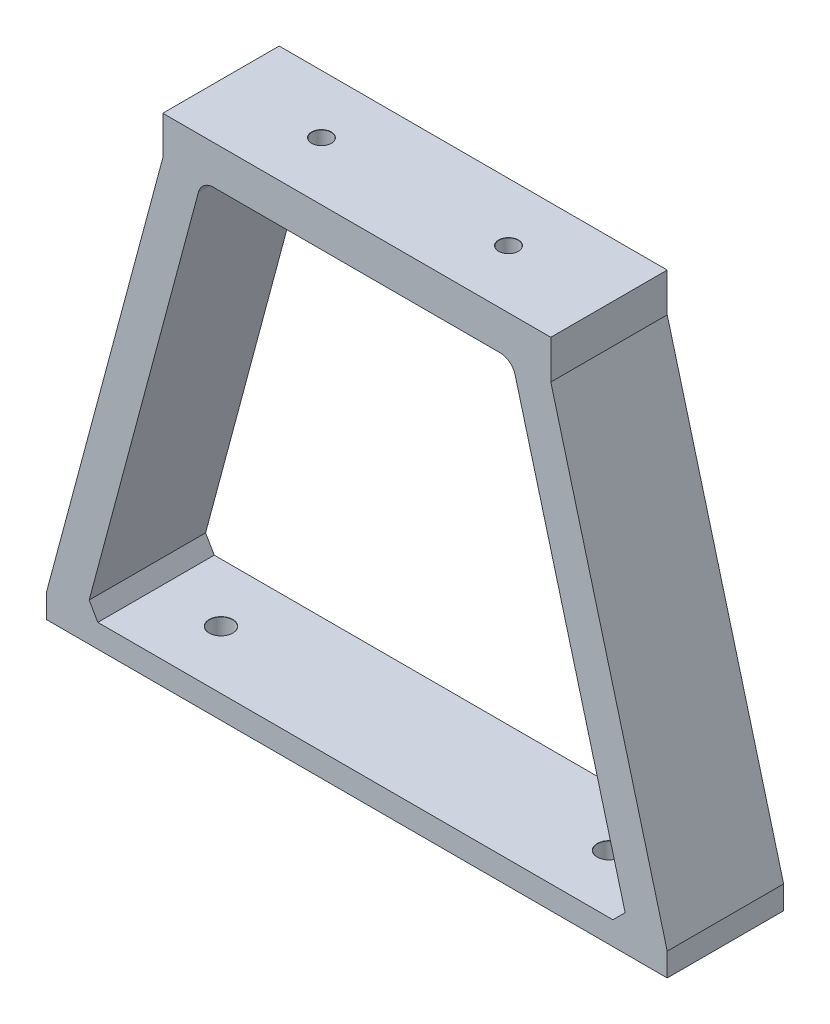
SolidWorks part; units mm, degrees
material "ABS"
ref_plane "Front Plane" through (0, 0, 0) normal (0, 0, 1) x (1, 0, 0)
ref_plane "Top Plane" through (0, 0, 0) normal (0, 1, 0) x (1, 0, 0)
ref_plane "Right Plane" through (0, 0, 0) normal (1, 0, 0) x (0, 0, -1)
sketch "Sketch1" plane through (0, 0, 0) normal (0, 1, 0) x (1, 0, 0)
  line L1 (-25, 7.5) -> (25, 7.5)
  line L2 (-25, 7.5) -> (-25, -7.5)
  line L3 (-25, -7.5) -> (25, -7.5)
  line L4 (25, 7.5) -> (25, -7.5)
  line L5 (-25, 7.5) -> (25, -7.5) construction
  line L6 (-25, -7.5) -> (25, 7.5) construction
  point P0 (0, 0)
  dimension "D1" = 15
  dimension "D2" = 50
extrude "Boss-Extrude1" add sketch "Sketch1" along normal blind 5
sketch "Sketch2" plane through (0, 0, 7.5) normal (0, 0, 1) x (1, 0, 0)
  line L0 (25, 0) -> (40, -56)
  line L1 (40, -56) -> (35, -56)
  line L2 (35, -56) -> (20, 0)
  line L3 (-25, 0) -> (25, 0) construction
  line L4 (20, 0) -> (25, 0)
  line L5 (-25, 0) -> (-40, -56)
  line L6 (-40, -56) -> (-35, -56)
  line L7 (-35, -56) -> (-20, 0)
  line L8 (-20, 0) -> (-25, 0)
  line L9 (0, -7.9912) -> (0, 3.1665) construction
  point P15 (0, 0)
  dimension "D1" = 56
  dimension "D2" = 5
  dimension "D3" = 80
extrude "Boss-Extrude2" add sketch "Sketch2" against normal up to surface (15 mm away) up to face at (0, 2.5, -7.5)
fillet "Fillet1" radius 2 2 edges at (20, 0, 0) (-20, 0, 0)
sketch "Sketch3" plane through (0, -56, 0) normal (0, -1, 0) x (1, 0, 0)
  line L1 (-40, 7.5) -> (40, 7.5)
  line L2 (-40, 7.5) -> (-40, -7.5)
  line L3 (-40, -7.5) -> (40, -7.5)
  line L4 (40, 7.5) -> (40, -7.5)
extrude "Boss-Extrude3" add sketch "Sketch3" along normal blind 3
chamfer "Chamfer1" distance 2 angle 45 2 edges at (35, -56, 0) (-35, -56, 0)
hole_wizard "Ø3.0mm Dowel Hole1" positions "Sketch4" profile "Sketch5" hole size "Ø3.0" standard "ANSI Metric"
sketch "Sketch4" plane through (0, -56, 0) normal (0, 1, 0) x (1, 0, 0)
  line L1 (0, 21.8102) -> (0, -19.5498) construction
  point P0 (-25, 0)
  point P2 (25, 0)
  point P16 (0, 0)
  dimension "D1" = 50
sketch "Sketch5" plane through (-25, -56, 0) normal (1, 0, 0) x (0, 0, 1)
  line L0 (0, 0) -> (0, 20.9013)
  line L1 (0, 20.9013) -> (1.5, 20)
  line L2 (1.5, 20) -> (1.5, 0.025)
  line L3 (1.5, 0.025) -> (1.525, 0)
  line L5 (1.525, 0) -> (0, 0)
  line L6 (-1.5, 0.025) -> (-1.525, 0) construction
  line L10 (0, 20.9013) -> (-1.5, 20) construction
  line L11 (0, -6.35) -> (0, 107.95) construction
  dimension "Hole Dia." = 3
  dimension "Hole Depth" = 20
  dimension "Near C'Sink Dia." = 3.05
  dimension "Near C'Sink Angle" = 90
  dimension "Drill Angle" = 118
hole_wizard "Ø2.5mm Dowel Hole1" positions "Sketch6" profile "Sketch7" hole size "Ø2.5" standard "ANSI Metric"
sketch "Sketch6" plane through (0, 5, 0) normal (0, 1, 0) x (1, 0, 0)
  point P0 (-12.05, 0)
  point P3 (12.05, 0)
sketch "Sketch7" plane through (-12.05, 5, 0) normal (1, 0, 0) x (0, 0, 1)
  line L0 (0, 0) -> (0, 20.7511)
  line L1 (0, 20.7511) -> (1.25, 20)
  line L2 (1.25, 20) -> (1.25, 0.025)
  line L3 (1.25, 0.025) -> (1.275, 0)
  line L5 (1.275, 0) -> (0, 0)
  line L6 (-1.25, 0.025) -> (-1.275, 0) construction
  line L10 (0, 20.7511) -> (-1.25, 20) construction
  line L11 (0, -6.35) -> (0, 107.95) construction
  dimension "Hole Dia." = 2.5
  dimension "Hole Depth" = 20
  dimension "Near C'Sink Dia." = 2.55
  dimension "Near C'Sink Angle" = 90
  dimension "Drill Angle" = 118
